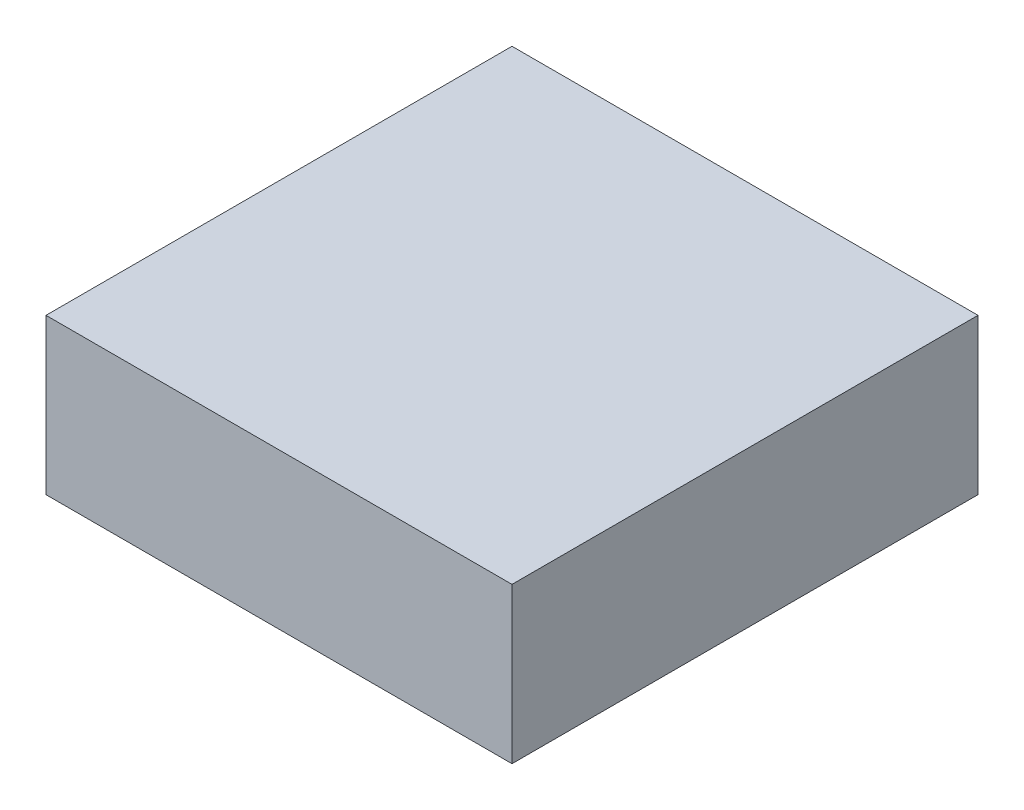
SolidWorks part; units mm, degrees
ref_plane "Front Plane" through (0, 0, 0) normal (0, 0, 1) x (1, 0, 0)
ref_plane "Top Plane" through (0, 0, 0) normal (0, 1, 0) x (1, 0, 0)
ref_plane "Right Plane" through (0, 0, 0) normal (1, 0, 0) x (0, 0, -1)
sketch "Sketch1" plane through (0, 0, 0) normal (0, 1, 0) x (1, 0, 0)
  line L0 (-15, 15) -> (15, -15) construction
  line L1 (-15, 15) -> (15, 15)
  line L2 (-15, 15) -> (-15, -15)
  line L3 (-15, -15) -> (15, -15)
  line L4 (15, 15) -> (15, -15)
  dimension "D1" = 30
  dimension "D2" = 30
extrude "Boss-Extrude1" add sketch "Sketch1" along normal blind 10
